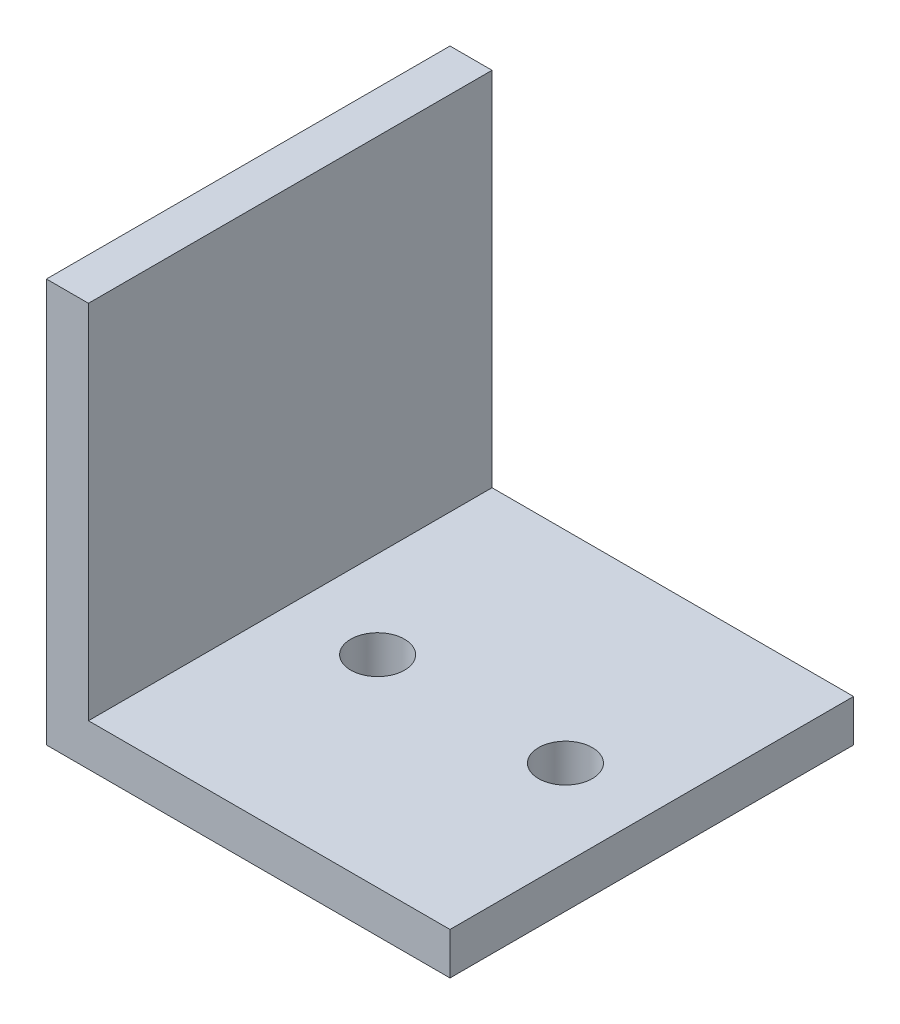
SolidWorks part; units mm, degrees
ref_plane "Plano frontal" through (0, 0, 0) normal (0, 0, 1) x (1, 0, 0)
ref_plane "Plano superior" through (0, 0, 0) normal (0, 1, 0) x (1, 0, 0)
ref_plane "Plano direito" through (0, 0, 0) normal (1, 0, 0) x (0, 0, -1)
sketch "Esboço1" plane through (0, 0, 0) normal (0, 0, 1) x (1, 0, 0)
  line L0 (0, 0) -> (-30, 0)
  line L1 (-30, 0) -> (-30, 30)
extrude "Extrusão-Fina1" add sketch "Esboço1" along normal blind 30 thin
sketch "Esboço2" plane through (0, 3.125, 0) normal (0, 1, 0) x (1, 0, 0)
  circle A0 centre (-6.4177, -15) radius 2
  circle A1 centre (-20.3809, -15) radius 2
extrude "Corte-extrusão1" cut sketch "Esboço2" against normal blind 30
